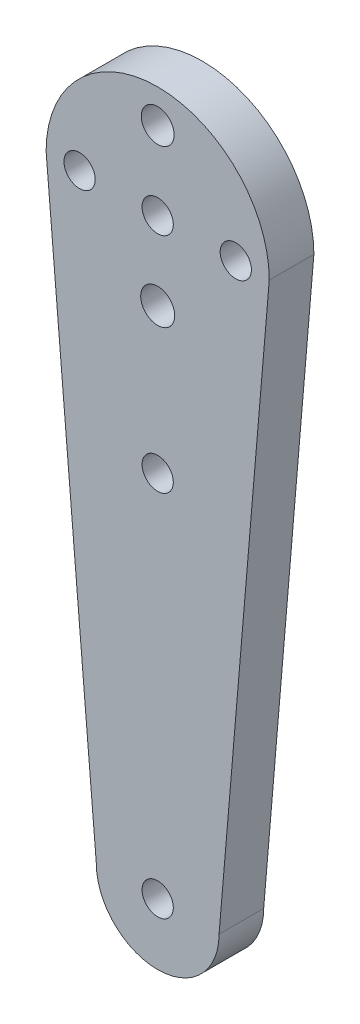
SolidWorks part; units mm, degrees
ref_plane "Front Plane" through (0, 0, 0) normal (0, 0, 1) x (1, 0, 0)
ref_plane "Top Plane" through (0, 0, 0) normal (0, 1, 0) x (1, 0, 0)
ref_plane "Right Plane" through (0, 0, 0) normal (1, 0, 0) x (0, 0, -1)
sketch "Sketch1" plane through (0, 0, 0) normal (0, 0, 1) x (1, 0, 0)
  line L8 (-5.5007, 45.0161) -> (-5.5007, 52.0236) construction
  line L10 (-15.5007, 45.0161) -> (-11.0007, -8.0067)
  line L11 (-0.0007, -8.0067) -> (4.4993, 45.0161)
  arc A1 (-11.0007, -8.0067) -> (-0.0007, -8.0067) centre (-5.5007, -8.0067) ccw
  circle A3 centre (-5.5007, -8.0067) radius 1.4
  circle A4 centre (-5.5007, 45.0161) radius 1.4
  arc A6 (4.4993, 45.0161) -> (-15.5007, 45.0161) centre (-5.5007, 45.0161) ccw
  circle A8 centre (1.4993, 45.0161) radius 1.4
  circle A9 centre (-12.5007, 45.0161) radius 1.4
  point P8 (-5.0007, -13.4839)
  dimension "D1" = 20
  dimension "D4" = 11
  dimension "D5" = 7
  dimension "D2" = 2.8
  dimension "D3" = 2.8
  dimension "D6" = 2.8
extrude "Boss-Extrude1" add sketch "Sketch1" along normal blind 4
sketch "Sketch2" plane through (0, 0, 4) normal (0, 0, 1) x (1, 0, 0)
  line L0 (-5.5007, 45.0161) -> (-5.5007, 26.4978) construction
  circle A0 centre (-5.5007, 38.0161) radius 1.5217
  circle A1 centre (-5.5007, 52.0161) radius 1.4726
  dimension "D1" = 7
  dimension "D2" = 7
extrude "Cut-Extrude1" cut sketch "Sketch2" against normal blind 10
sketch "Sketch3" plane through (0, 0, 4) normal (0, 0, 1) x (1, 0, 0)
  line L0 (-5.5007, 45.0161) -> (-5.5007, 12.3076) construction
  circle A0 centre (-5.5007, 25.0161) radius 1.4
  dimension "D1" = 2.8
  dimension "D2" = 20
extrude "Cut-Extrude2" cut sketch "Sketch3" against normal blind 10
